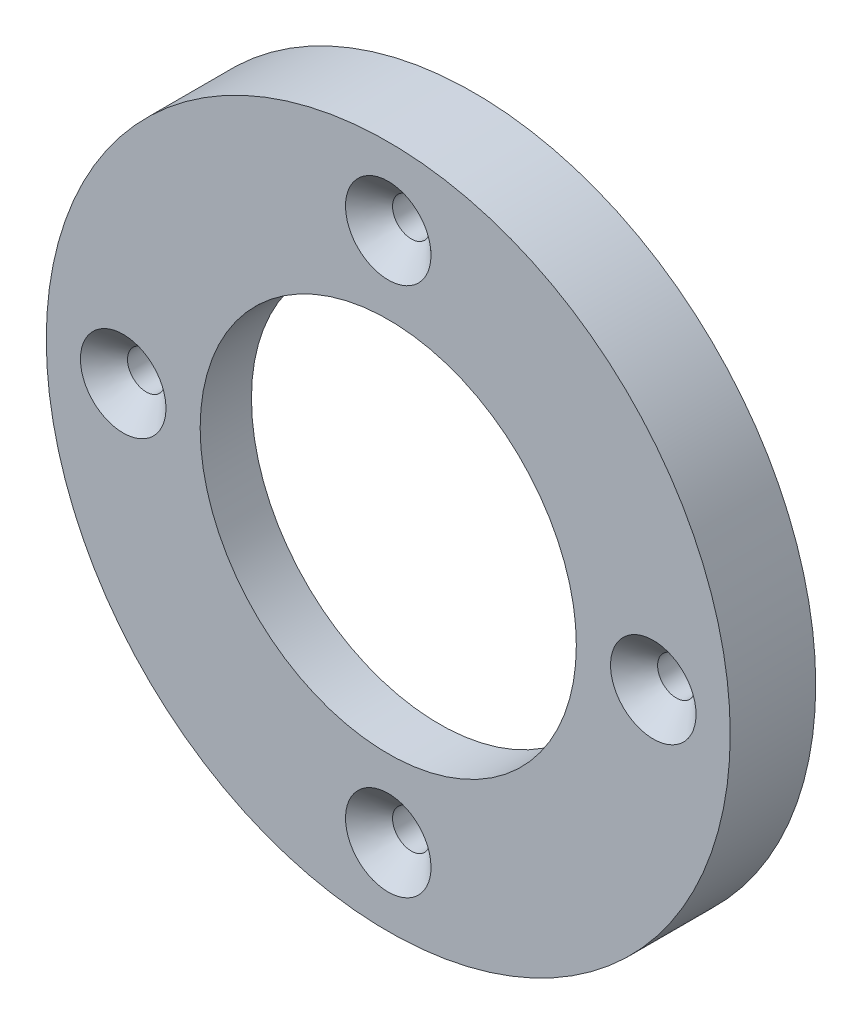
SolidWorks part; units mm, degrees
material "ABS"
ref_plane "Спереди" through (0, 0, 0) normal (0, 0, 1) x (1, 0, 0)
ref_plane "Сверху" through (0, 0, 0) normal (0, 1, 0) x (1, 0, 0)
ref_plane "Справа" through (0, 0, 0) normal (1, 0, 0) x (0, 0, -1)
sketch "Эскиз1" plane through (0, 0, 0) normal (0, 0, 1) x (1, 0, 0)
  arc A0 (-17.6855, -3.3502) -> (-3.3502, -17.6855) centre (0, 0) ccw
  circle A1 centre (0, 0) radius 15.5 construction
  arc A6 (-3.3502, 17.6855) -> (-17.6855, -3.3502) centre (0, 0) ccw
  arc A7 (17.6855, -3.3502) -> (-3.3502, 17.6855) centre (0, 0) ccw
  arc A8 (-3.3502, -17.6855) -> (17.6855, -3.3502) centre (0, 0) ccw
  point P18 (0, 0)
  dimension "D1" = 36
  dimension "D2" = 31
extrude "Бобышка-Вытянуть1" add sketch "Эскиз1" along normal blind 3
sketch "Эскиз2" plane through (0, 0, 3) normal (0, 0, 1) x (1, 0, 0)
  circle A0 centre (0, 0) radius 11
  dimension "D1" = 22
extrude "Вырез-Вытянуть1" cut sketch "Эскиз2" against normal through all
sketch "Эскиз3" plane through (0, 0, 3) normal (0, 0, 1) x (1, 0, 0)
  circle A0 centre (-15.5, 0) radius 2.2
  point P12 (0, 0)
  dimension "D1" = 4.4
  dimension "D2" = 15.5
sketch "Эскиз5" plane through (0, 0, 3) normal (0, 0, 1) x (1, 0, 0)
  circle A0 centre (0, 0) radius 18
  circle A1 centre (0, 0) radius 20
  dimension "D1" = 36
  dimension "D2" = 40
extrude "Бобышка-Вытянуть2" add sketch "Эскиз5" against normal blind 5
ref_axis "Ось1" through (-15.5, 0, -24.0809) along (0, 0, 1)
sketch "Эскиз6" plane through (0, 0, 0) normal (0, 1, 0) x (1, 0, 0)
  line L0 (-16.6, -1.648) -> (-18, -3)
  line L1 (-18, -3) -> (-15.5, -3)
  line L2 (-15.5, -1.648) -> (-15.5, -3)
  line L3 (-16.6, -1.648) -> (-16.6, 2)
  line L4 (-16.6, 2) -> (-15.5, 2)
  line L5 (-15.5, 2) -> (-15.5, -1.648)
  line L7 (-15.5, 24.0809) -> (-15.5, -65.7688) construction
  line L9 (20, 2) -> (-20, 2) construction
  line L10 (-17.7, -3) -> (-13.3, -3) construction
  point P6 (-15.5, -3)
  point P14 (-15.5, 2)
  dimension "D1" = 1.1
  dimension "D2" = 46
  dimension "D4" = 2.5
revolve "Вырез-Повернуть1" cut sketch "Эскиз6" angle 360 about axis through (-15.5, 0, -24.0809) along (0, 0, 1)
pattern_circular "Круговой массив1" count 4 over 360 about axis through (0, 0, 0) along (0, 0, 1) of "Вырез-Повернуть1"
chamfer "Фаска1" distance 0.5 angle 45 1 edges at (18, 0, -2)
